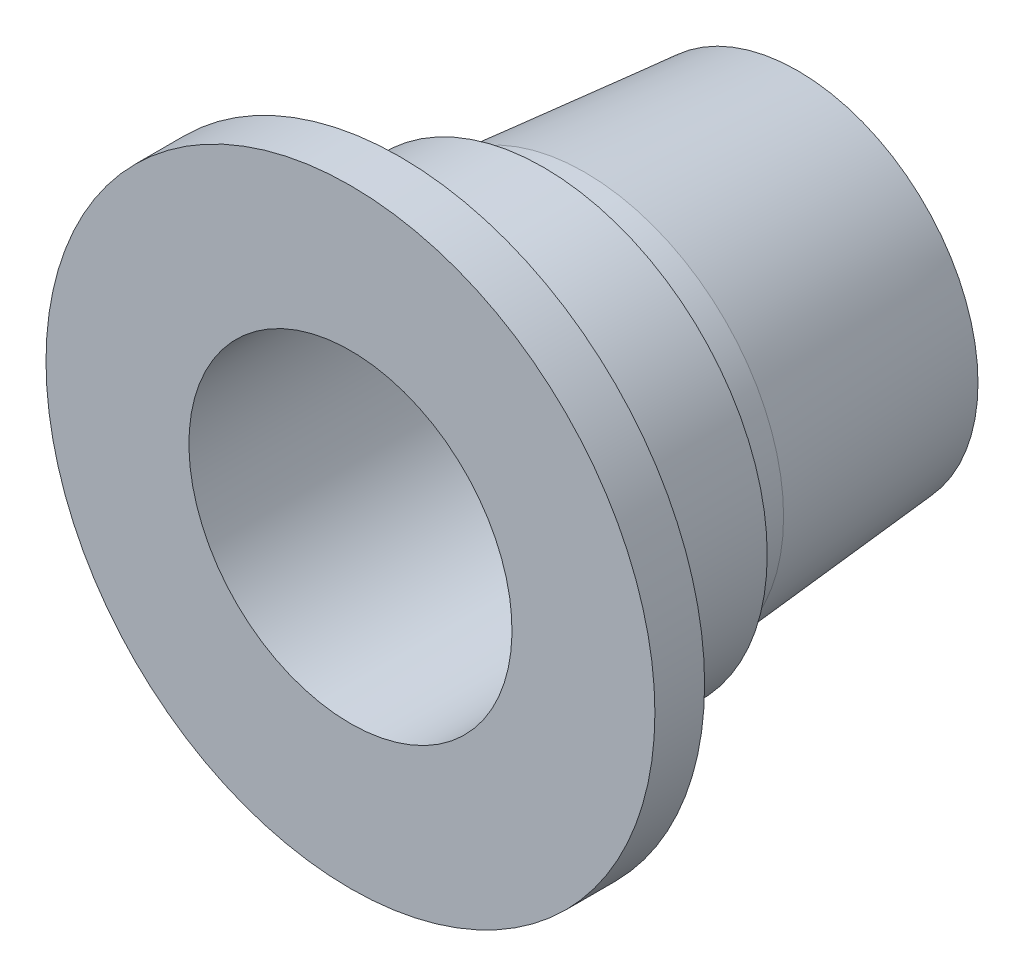
SolidWorks part; units mm, degrees
material "1060 Сплав"
ref_plane "Спереди" through (0, 0, 0) normal (0, 0, 1) x (1, 0, 0)
ref_plane "Сверху" through (0, 0, 0) normal (0, 1, 0) x (1, 0, 0)
ref_plane "Справа" through (0, 0, 0) normal (1, 0, 0) x (0, 0, -1)
sketch "Эскиз1" plane through (0, 0, 0) normal (1, 0, 0) x (0, 0, -1)
  line L0 (0, 13) -> (36, 13)
  line L1 (36, 13) -> (36, 14.5)
  line L2 (36, 14.5) -> (18.8549, 16)
  line L3 (18.8549, 16) -> (16, 16)
  line L4 (16, 16) -> (16, 18)
  line L5 (16, 18) -> (7, 18)
  line L6 (7, 18) -> (7, 16)
  line L7 (7, 16) -> (4, 16)
  line L8 (4, 16) -> (4, 24.5)
  line L9 (4, 24.5) -> (0, 24.5)
  line L10 (0, 24.5) -> (0, 13)
  line L11 (0, 0) -> (47.8862, 0) construction
  dimension "D1" = 26
  dimension "D2" = 32
  dimension "D3" = 49
  dimension "D4" = 36
  dimension "D5" = 4
  dimension "D6" = 3
  dimension "D7" = 5
  dimension "D8" = 16
  dimension "D9" = 36
  dimension "D10" = 29
revolve "Повернуть1" add sketch "Эскиз1" angle 360 about L11
cosmetic thread "Условное изображение резьбы1" parameters "D2"=33.797
chamfer "Фаска1" distance 0.8 angle 30 2 edges at (0, -18, -16) (0, -18, -7)
